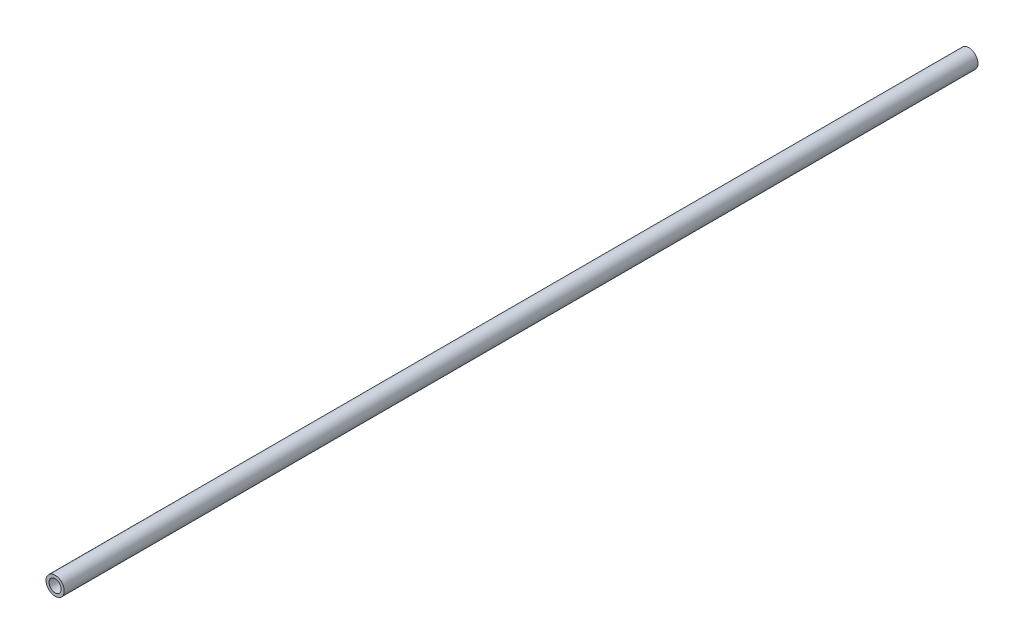
SolidWorks part; units mm, degrees
material "PVC Rigid"
ref_plane "Front Plane" through (0, 0, 0) normal (0, 0, 1) x (1, 0, 0)
ref_plane "Top Plane" through (0, 0, 0) normal (0, 1, 0) x (1, 0, 0)
ref_plane "Right Plane" through (0, 0, 0) normal (1, 0, 0) x (0, 0, -1)
sketch "Sketch1" plane through (0, 0, 0) normal (0, 0, 1) x (1, 0, 0)
  circle A0 centre (0, 0) radius 7.62
  circle A2 centre (0, 0) radius 5.08
  dimension "D1" = 15.24
  dimension "D2" = 10.16
extrude "Boss-Extrude1" add sketch "Sketch1" along normal blind 762
